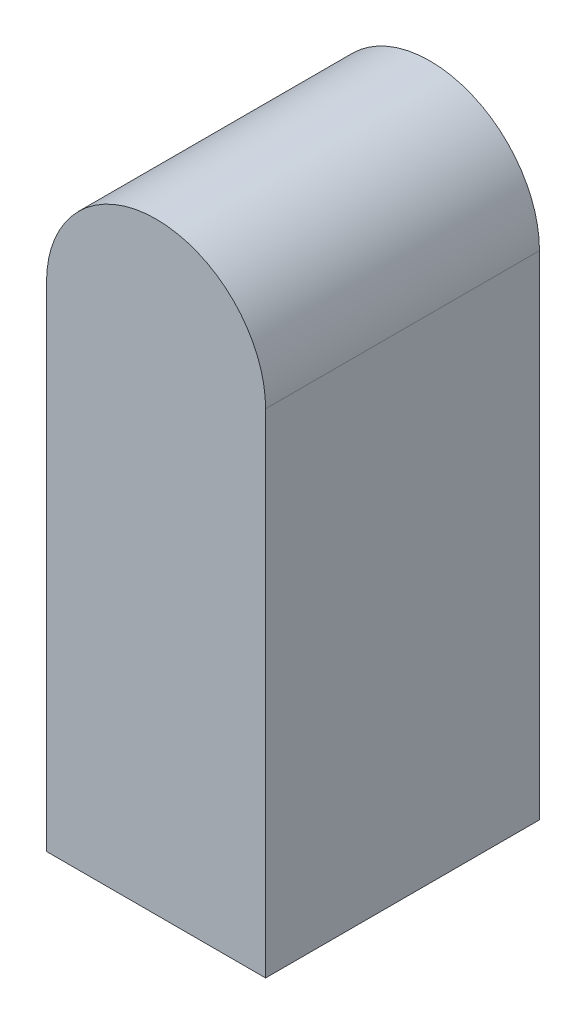
SolidWorks part; units mm, degrees
ref_plane "Piano frontale" through (0, 0, 0) normal (0, 0, 1) x (1, 0, 0)
ref_plane "Piano superiore" through (0, 0, 0) normal (0, 1, 0) x (1, 0, 0)
ref_plane "Piano destro" through (0, 0, 0) normal (1, 0, 0) x (0, 0, -1)
sketch "Schizzo1" plane through (0, 0, 0) normal (0, 0, 1) x (1, 0, 0)
  line L2 (-40, 0) -> (-40, -180)
  line L3 (-40, -180) -> (40, -180)
  line L4 (40, 0) -> (40, -180)
  arc A0 (40, 0) -> (-40, 0) centre (0, 0) ccw
  dimension "D1" = 80
  dimension "D2" = 180
extrude "Estrusione-Estrusione1" add sketch "Schizzo1" along normal blind 100
